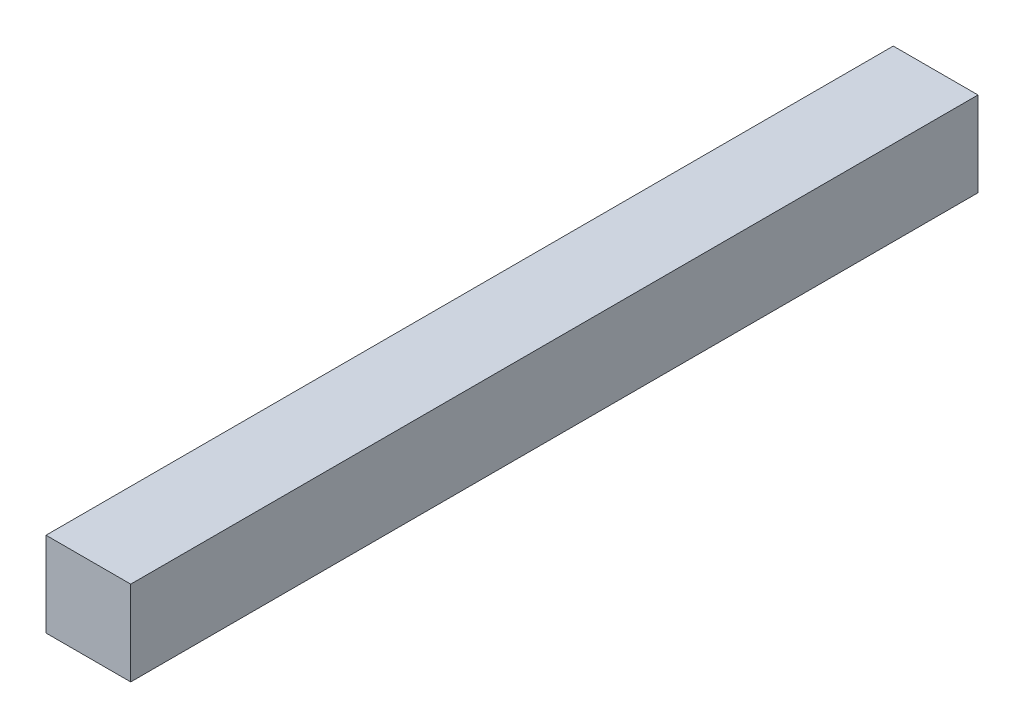
SolidWorks part; units mm, degrees
ref_plane "Front" through (0, 0, 0) normal (0, 0, 1) x (1, 0, 0)
ref_plane "Top" through (0, 0, 0) normal (0, 1, 0) x (1, 0, 0)
ref_plane "Right" through (0, 0, 0) normal (1, 0, 0) x (0, 0, -1)
sketch "Sketch1" plane through (0, 0, 0) normal (0, 0, 1) x (1, 0, 0)
  line L1 (0, 0) -> (3, 0)
  line L2 (0, 0) -> (0, 3)
  line L3 (0, 3) -> (3, 3)
  line L4 (3, 0) -> (3, 3)
  dimension "D1" = 3
  dimension "D2" = 3
extrude "Boss-Extrude1" add sketch "Sketch1" along normal blind 30 contours L3 L4 L1 L2
